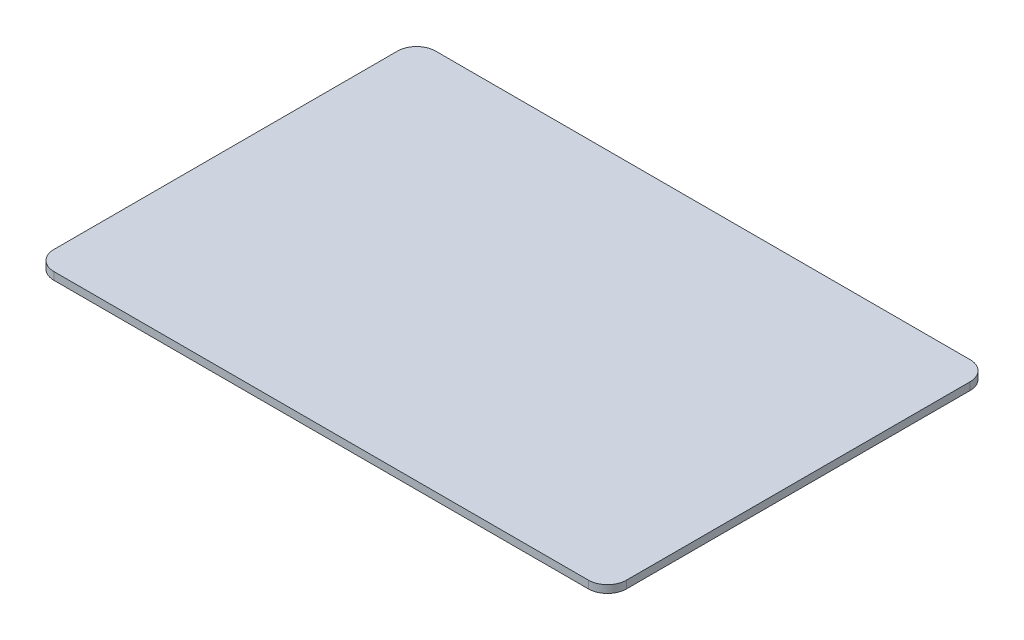
SolidWorks part; units mm, degrees
ref_plane "Front Plane" through (0, 0, 0) normal (0, 0, 1) x (1, 0, 0)
ref_plane "Top Plane" through (0, 0, 0) normal (0, 1, 0) x (1, 0, 0)
ref_plane "Right Plane" through (0, 0, 0) normal (1, 0, 0) x (0, 0, -1)
sketch "Sketch1" plane through (0, 0, 0) normal (0, 1, 0) x (1, 0, 0)
  line L1 (140, -100) -> (-140, -100)
  line L2 (150, -90) -> (150, 90)
  line L3 (140, 100) -> (-140, 100)
  line L4 (-150, -90) -> (-150, 90)
  line L5 (150, -100) -> (-150, 100) construction
  line L6 (150, 100) -> (-150, -100) construction
  arc A0 (140, -100) -> (150, -90) centre (140, -90) ccw
  arc A1 (-140, -100) -> (-150, -90) centre (-140, -90) cw
  arc A2 (150, 90) -> (140, 100) centre (140, 90) ccw
  arc A3 (-140, 100) -> (-150, 90) centre (-140, 90) ccw
  point P0 (0, 0)
  dimension "D3" = 10
  dimension "D1" = 300
  dimension "D2" = 200
extrude "Boss-Extrude1" add sketch "Sketch1" along normal blind 4
